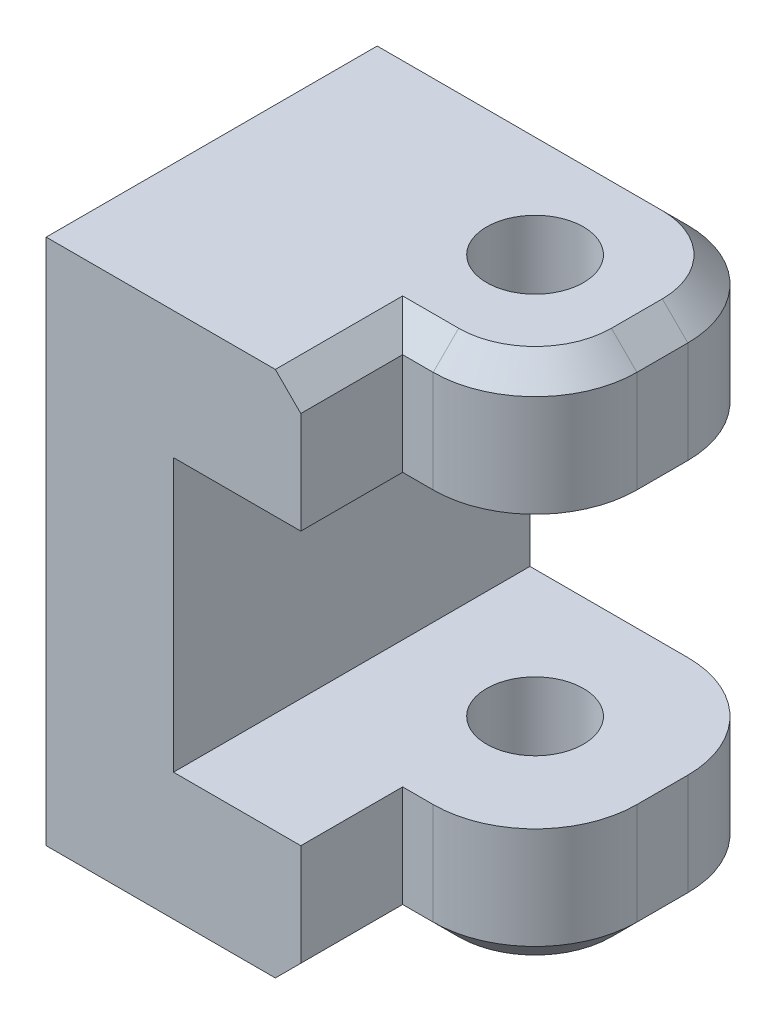
SolidWorks part; units mm, degrees
ref_plane "正面(Front)" through (0, 0, 0) normal (0, 0, 1) x (1, 0, 0)
ref_plane "平面(Top)" through (0, 0, 0) normal (0, 1, 0) x (1, 0, 0)
ref_plane "右側面(Right)" through (0, 0, 0) normal (1, 0, 0) x (0, 0, -1)
sketch "ｽｹｯﾁ1" plane through (0, 0, 0) normal (0, 0, 1) x (1, 0, 0)
  circle A0 centre (0, 0) radius 6.25
  dimension "D1" = 12.5
extrude "ﾎﾞｽ - 押し出し1" add sketch "ｽｹｯﾁ1" against normal blind 15
sketch "ｽｹｯﾁ2" plane through (0, 0, 0) normal (0, 0, 1) x (1, 0, 0)
  line L1 (-14.75, 10.35) -> (14.75, 10.35)
  line L2 (-14.75, 10.35) -> (-14.75, -10.35)
  line L3 (-14.75, -10.35) -> (14.75, -10.35)
  line L4 (14.75, 10.35) -> (14.75, -10.35)
  line L5 (-14.75, 10.35) -> (14.75, -10.35) construction
  line L6 (-14.75, -10.35) -> (14.75, 10.35) construction
  point P0 (0, 0)
  dimension "D1" = 20.7
  dimension "D2" = 29.5
extrude "ﾎﾞｽ - 押し出し2" add sketch "ｽｹｯﾁ2" along normal blind 5
sketch "ｽｹｯﾁ3" plane through (14.75, 0, 0) normal (1, 0, 0) x (0, 0, -1)
  line L0 (0, 0) -> (-31.0876, 0) construction
  line L1 (-5, 10.35) -> (-44, 10.35)
  line L3 (-44, 10.35) -> (-44, -10.35)
  line L6 (-5, -10.35) -> (-44, -10.35)
  line L7 (-5, 10.35) -> (-5, -10.35)
  circle A0 centre (-20, 0) radius 1.6
  dimension "D2" = 15
  dimension "D4" = 3.2
  dimension "D1" = 39
extrude "ﾎﾞｽ - 押し出し3" add sketch "ｽｹｯﾁ3" against normal blind 5
sketch "ｽｹｯﾁ4" plane through (14.75, 0, 0) normal (1, 0, 0) x (0, 0, -1)
  line L1 (0, 10.35) -> (-10, 10.35)
  line L2 (0, 10.35) -> (0, 5.35)
  line L3 (0, 5.35) -> (-10, 5.35)
  line L4 (-10, 10.35) -> (-10, 5.35)
  line L5 (0, -10.35) -> (-10, -10.35)
  line L6 (0, -10.35) -> (0, -5.35)
  line L7 (0, -5.35) -> (-10, -5.35)
  line L8 (-10, -10.35) -> (-10, -5.35)
  line L9 (-44, 10.35) -> (-34, 10.35)
  line L10 (-44, 10.35) -> (-44, 5.35)
  line L11 (-44, 5.35) -> (-34, 5.35)
  line L12 (-34, 10.35) -> (-34, 5.35)
  line L13 (-44, -10.35) -> (-34, -10.35)
  line L14 (-44, -10.35) -> (-44, -5.35)
  line L15 (-44, -5.35) -> (-34, -5.35)
  line L16 (-34, -10.35) -> (-34, -5.35)
  dimension "D1" = 5
  dimension "D2" = 5
  dimension "D3" = 10
  dimension "D4" = 10
extrude "ﾎﾞｽ - 押し出し4" add sketch "ｽｹｯﾁ4" along normal blind 10.2
sketch "ｽｹｯﾁ5" plane through (0, -10.35, 0) normal (0, -1, 0) x (1, 0, 0)
  line L4 (24.95, 5) -> (5.2641, 5) construction
  line L5 (24.95, 10) -> (24.95, 0) construction
  line L6 (24.95, 39) -> (4.1235, 39) construction
  line L7 (24.95, 44) -> (24.95, 34) construction
  circle A0 centre (19.95, 5) radius 1.9
  circle A2 centre (19.95, 39) radius 1.9
  dimension "D1" = 3.8
  dimension "D2" = 5
extrude "ｶｯﾄ - 押し出し1" cut sketch "ｽｹｯﾁ5" against normal through all
fillet "ﾌｨﾚｯﾄ1" radius 4 8 edges at (24.95, 7.85, 10) (24.95, 7.85, 0) (24.95, -7.85, 0) (24.95, -7.85, 10) (24.95, -7.85, 34) (24.95, 7.85, 34) (24.95, 7.85, 44) (24.95, -7.85, 44)
sketch "ｽｹｯﾁ8" plane through (14.75, 0, 0) normal (1, 0, 0) x (0, 0, -1)
  line L1 (-34, 10.35) -> (-10, 10.35)
  line L2 (-34, 10.35) -> (-34, 5.35)
  line L3 (-34, 5.35) -> (-10, 5.35)
  line L4 (-10, 10.35) -> (-10, 5.35)
  line L5 (-34, -5.35) -> (-10, -5.35)
  line L6 (-34, -5.35) -> (-34, -10.35)
  line L7 (-34, -10.35) -> (-10, -10.35)
  line L8 (-10, -5.35) -> (-10, -10.35)
extrude "ﾎﾞｽ - 押し出し6" add sketch "ｽｹｯﾁ8" along normal blind 5
sketch "ｽｹｯﾁ9" plane through (-14.75, 0, 0) normal (-1, 0, 0) x (0, 0, 1)
  line L0 (0, 0) -> (29.5336, 0) construction
  line L1 (5, 10.35) -> (11, 10.35)
  line L2 (5, 10.35) -> (44, 10.35) construction
  line L3 (11, 10.35) -> (22.1218, 3.3909)
  line L4 (11, -10.35) -> (22.1218, -3.3909)
  line L5 (5, -10.35) -> (11, -10.35)
  line L6 (5, -10.35) -> (5, 10.35)
  arc A0 (22.1218, 3.3909) -> (22.1218, -3.3909) centre (20, 0) cw
  circle A2 centre (20, 0) radius 1.6 construction
  circle A3 centre (20, 0) radius 1.6
  dimension "D1" = 4
  dimension "D3" = 3.2
  dimension "D2" = 6
extrude "ﾎﾞｽ - 押し出し7" add sketch "ｽｹｯﾁ9" against normal blind 5
sketch "ｽｹｯﾁ6" plane through (0, -10.35, 0) normal (0, -1, 0) x (1, 0, 0)
  line L3 (-9.75, 5) -> (9.75, 5) construction
  line L8 (9.75, 44) -> (9.75, 5) construction
  line L9 (-9.75, 5) -> (9.75, 5)
  line L10 (9.75, 5) -> (9.75, 15)
  line L11 (-9.75, 5) -> (9.75, 5) construction
  line L12 (-9.75, 5) -> (-9.75, 8)
  line L13 (-9.75, 5) -> (-9.75, 11) construction
  line L15 (-9.75, 8) -> (-2.3744, 8)
  line L16 (-2.3744, 8) -> (9.75, 15)
  dimension "D1" = 30
  dimension "D2" = 10
extrude "ﾎﾞｽ - 押し出し5" add sketch "ｽｹｯﾁ6" against normal blind 3
mirror "ﾐﾗｰ1" about plane through (0, 0, 0) normal (0, 1, 0) of "ﾎﾞｽ - 押し出し5"
chamfer "面取り1" distance 1 angle 45 28 edges at (19.75, 10.35, 22) (20.35, 10.35, 10) (23.7784, 10.35, 8.8284) (24.95, 10.35, 5) (23.7784, 10.35, 1.1716) (3.1, 10.35, 0) (-14.75, 10.35, 5.5) (-14.75, 0, 0) (-14.75, -10.35, 5.5) (20.35, -10.35, 10) (3.1, -10.35, 0) (23.7784, -10.35, 8.8284) (23.7784, -10.35, 1.1716) (24.95, -10.35, 5) (19.75, -10.35, 22) (20.35, 10.35, 34) (20.35, -10.35, 34) (23.7784, 10.35, 35.1716) (23.7784, -10.35, 35.1716) (24.95, 10.35, 39) (24.95, -10.35, 39) (23.7784, 10.35, 42.8284) (23.7784, -10.35, 42.8284) (15.35, 10.35, 44) (15.35, -10.35, 44) (9.75, 10.35, 29.5) (9.75, 0, 44) (9.75, -10.35, 29.5)
chamfer "面取り2" distance 1 angle 45 2 edges at (-9.75, 8.85, 8) (-9.75, -8.85, 8)
sketch "ｽｹｯﾁ10" plane through (14.75, 0, 0) normal (1, 0, 0) x (0, 0, -1)
  line L1 (-23.15, 2.9) -> (-16.85, 2.9)
  line L2 (-23.15, 2.9) -> (-23.15, -2.9)
  line L3 (-23.15, -2.9) -> (-16.85, -2.9)
  line L4 (-16.85, 2.9) -> (-16.85, -2.9)
  line L5 (-23.15, 2.9) -> (-16.85, -2.9) construction
  line L6 (-23.15, -2.9) -> (-16.85, 2.9) construction
  point P0 (-20, 0)
  dimension "D1" = 5.8
  dimension "D2" = 6.3
extrude "ｶｯﾄ - 押し出し2" cut sketch "ｽｹｯﾁ10" against normal blind 2.5
sketch "ｽｹｯﾁ11" plane through (0, 0, 0) normal (1, 0, 0) x (0, 0, -1)
  line L0 (0, 0) -> (15, 0) construction
  line L1 (15, -6.25) -> (15, 6.25) construction
  line L2 (0, -6.25) -> (0, 6.25) construction
  circle A0 centre (7.5, 0) radius 1.65
  dimension "D1" = 3.3
  dimension "D2" = 7.5
extrude "ｶｯﾄ - 押し出し3" cut sketch "ｽｹｯﾁ11" against normal through all both and the other way through all
sketch "ｽｹｯﾁ12" plane through (0, 10.35, 0) normal (0, 1, 0) x (1, 0, 0)
  line L0 (29.9329, -14) -> (9.75, -14)
  line L1 (9.75, -14) -> (9.75, 2.8154)
  line L2 (9.75, -43) -> (9.75, -15) construction
  line L3 (20.95, -10) -> (19.75, -10) construction
  dimension "D1" = 4
extrude "ｶｯﾄ - 押し出し4" cut sketch "ｽｹｯﾁ12" against normal through all and the other way through all
